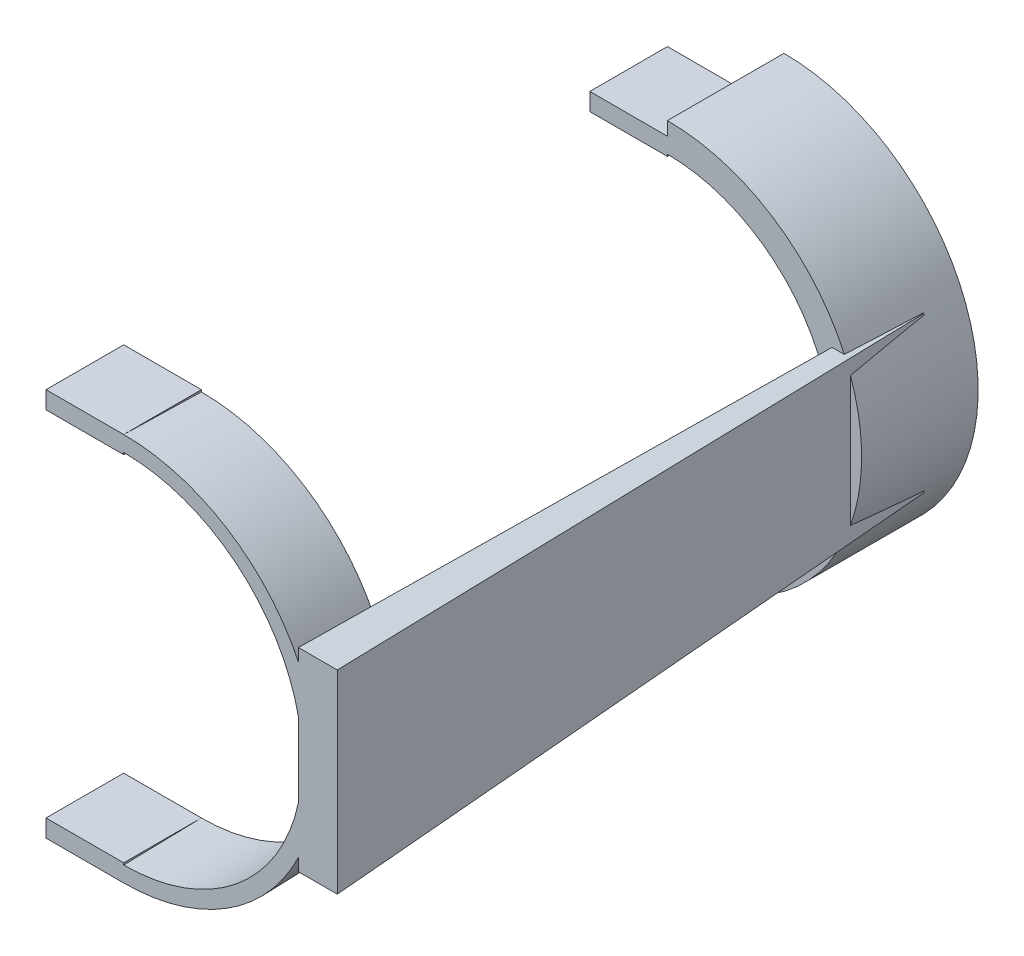
SolidWorks part; units mm, degrees
ref_plane "Front" through (0, 0, 0) normal (0, 0, 1) x (1, 0, 0)
ref_plane "Top" through (0, 0, 0) normal (0, 1, 0) x (1, 0, 0)
ref_plane "Right" through (0, 0, 0) normal (1, 0, 0) x (0, 0, -1)
sketch "草图1" plane through (0, 0, 0) normal (1, 0, 0) x (0, 0, -1)
  line L0 (0, 46) -> (0, 75.0518) construction
  line L1 (0, 0) -> (-171.072, 0) construction
  line L2 (0, 50) -> (0, 46)
  line L3 (160, 42) -> (160, 46)
  line L4 (0, 0) -> (160, 0)
  line L5 (0, 50) -> (160, 46)
  line L6 (0, 46) -> (160, 42)
  point P7 (0, 46)
  point P8 (160, 42)
  dimension "D1" = 50
  dimension "D2" = 160
  dimension "D3" = 46
  dimension "D4" = 46
  dimension "D5" = 42
revolve "旋转1" add sketch "草图1" angle 180 about L4
sketch "草图2" plane through (0, 0, 0) normal (1, 0, 0) x (0, 0, -1)
  line L0 (0, 50) -> (0, -50) construction
  line L1 (160, 46) -> (160, -46) construction
  line L3 (20, 60.115) -> (140, 60.115)
  line L4 (20, 60.115) -> (20, -64.3514)
  line L5 (20, -64.3514) -> (140, -64.3514)
  line L6 (140, 60.115) -> (140, -64.3514)
  dimension "D1" = 20
  dimension "D2" = 20
extrude "切除-拉伸1" cut sketch "草图2" along normal through all
sketch "草图3" plane through (0, 0, 0) normal (0, 0, 1) x (1, 0, 0)
  line L0 (0, 0) -> (53.4175, 0) construction
  line L2 (55, 25) -> (45, 25)
  line L3 (55, 25) -> (55, -25)
  line L4 (55, -25) -> (45, -25)
  line L5 (45, 25) -> (45, -25)
  dimension "D1" = 50
  dimension "D2" = 25
  dimension "D3" = 10
  dimension "D4" = 55
sketch "草图4" plane through (0, 0, -160) normal (0, 0, -1) x (-1, 0, 0)
  line L0 (0, 0) -> (-66.5571, 0) construction
  line L2 (-46, 20) -> (-42, 20)
  line L3 (-46, 20) -> (-46, -20)
  line L4 (-46, -20) -> (-42, -20)
  line L5 (-42, 20) -> (-42, -20)
  dimension "D1" = 46
  dimension "D2" = 4
  dimension "D3" = 40
  dimension "D4" = 20
loft "放样1" add profiles "草图3", "草图4"
sketch "草图6" plane through (0, 0, 0) normal (-1, 0, 0) x (0, 0, 1)
  line L0 (-20, -45.5) -> (-20, -49.5) construction
  line L1 (-20, 45.5) -> (0, 45.5)
  line L2 (-20, 45.5) -> (-20, 50)
  line L3 (-20, 50) -> (0, 50)
  line L4 (0, 45.5) -> (0, 50)
  line L5 (0, -50) -> (-20, -50)
  line L6 (0, -50) -> (0, -45.5)
  line L7 (0, -45.5) -> (-20, -45.5)
  line L8 (-20, -50) -> (-20, -45.5)
  line L9 (0, -46) -> (-20, -45.5) construction
  line L11 (-140, -46.5) -> (-160, -46.5)
  line L12 (-140, -46.5) -> (-140, -42)
  line L13 (-140, -42) -> (-160, -42)
  line L14 (-160, -46.5) -> (-160, -42)
  line L15 (-140, 46.5) -> (-160, 46.5)
  line L16 (-140, 46.5) -> (-140, 42)
  line L17 (-140, 42) -> (-160, 42)
  line L18 (-160, 46.5) -> (-160, 42)
extrude "凸台-拉伸1" add sketch "草图6" along normal blind 20
sketch "草图8" plane through (0, 0, -140) normal (0, 0, 1) x (1, 0, 0)
  line L0 (0, 46) -> (0, 50)
  line L1 (0, -46) -> (0, -50)
  arc A0 (0, -46) -> (0, 46) centre (0, 0) ccw
  arc A1 (0, -50) -> (0, 50) centre (0, 0) ccw
extrude "凸台-拉伸3" add sketch "草图8" against normal blind 30
